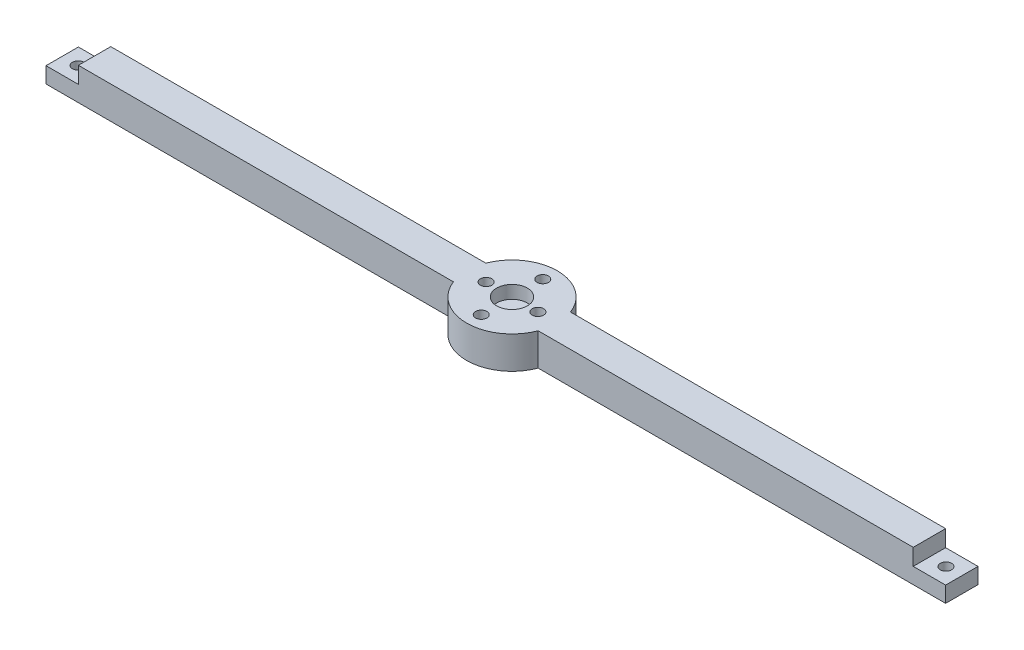
SolidWorks part; units mm, degrees
ref_plane "Front Plane" through (0, 0, 0) normal (0, 0, 1) x (1, 0, 0)
ref_plane "Top Plane" through (0, 0, 0) normal (0, 1, 0) x (1, 0, 0)
ref_plane "Right Plane" through (0, 0, 0) normal (1, 0, 0) x (0, 0, -1)
sketch "Sketch1" plane through (0, 0, 0) normal (0, 1, 0) x (1, 0, 0)
  circle A0 centre (0, 0) radius 14
  dimension "D1" = 28
extrude "Boss-Extrude1" add sketch "Sketch1" along normal blind 10
sketch "Sketch2" plane through (0, 10, 0) normal (0, 1, 0) x (1, 0, 0)
  line L0 (14, 0) -> (149, 0) construction
  line L1 (13.0767, -5) -> (149, -5)
  line L2 (13.0767, 5) -> (149, 5)
  line L4 (149, -5) -> (149, 5)
  line L5 (0, 5) -> (149, 5) construction
  line L6 (0, 0) -> (149, 0) construction
  line L7 (0, -5) -> (149, -5) construction
  circle A1 centre (0, 0) radius 14
  arc A2 (13.0767, -5) -> (13.0767, 5) centre (0, 0) ccw
  point P19 (0, 0)
  dimension "D1" = 149
  dimension "D2" = 5
  dimension "D3" = 5
  dimension "D4" = 0
extrude "Boss-Extrude2" add sketch "Sketch2" against normal up to surface (10 mm away) up to face at (0, 0, 14)
sketch "Sketch4" plane through (0, 0, 5) normal (0, 0, 1) x (1, 0, 0)
  line L0 (149, 0) -> (139, 0) construction
  line L1 (149, 0) -> (13.0767, 0) construction
  line L2 (139, 0) -> (139, 5) construction
  line L3 (139, 5) -> (129, 5) construction
  line L4 (129, 5) -> (129, 10) construction
  line L5 (13.0767, 10) -> (149, 10) construction
  line L6 (138.9, 0) -> (138.9, 4.9)
  line L7 (138.9, 4.9) -> (128.9, 4.9)
  line L8 (128.9, 4.9) -> (128.9, 10)
  line L9 (128.9, 10) -> (149, 10)
  line L10 (149, 10) -> (149, 0)
  line L11 (149, 0) -> (138.9, 0)
  dimension "D1" = 10
  dimension "D2" = 10
  dimension "D3" = 5
  dimension "D4" = 0.1
extrude "Cut-Extrude2" cut sketch "Sketch4" against normal through all
sketch "Sketch6" plane through (0, 4.9, 0) normal (0, 1, 0) x (1, 0, 0)
  line L0 (138.9, 5) -> (128.9, 5) construction
  line L1 (129, 5) -> (139, 5) construction
  line L2 (129, 5) -> (129, -5) construction
  line L3 (129, -5) -> (139, -5) construction
  line L4 (139, 5) -> (139, -5) construction
  line L5 (128.9, -5) -> (138.9, -5) construction
  line L6 (138.9, 5) -> (138.9, -5) construction
  line L7 (128.9, 5) -> (128.9, -5) construction
  line L8 (129, 5) -> (139, -5) construction
  circle A0 centre (134, 0) radius 1.75
  dimension "D3" = 3.5
  dimension "D1" = 0.1
  dimension "D2" = 0.1
extrude "Cut-Extrude4" cut sketch "Sketch6" against normal blind 10
pattern_circular "CirPattern2" count 2 over 180 about axis through (0, 0, 0) along (0, 1, 0) of "Boss-Extrude2", "Cut-Extrude2", "Cut-Extrude4"
sketch "Sketch5" plane through (0, 10, 0) normal (0, 1, 0) x (1, 0, 0)
  line L0 (-8, 0) -> (8, 0) construction
  line L1 (0, -9.5) -> (0, 9.5) construction
  circle A0 centre (0, 9.5) radius 1.75
  circle A1 centre (8, 0) radius 1.75
  circle A2 centre (-8, 0) radius 1.75
  circle A3 centre (0, -9.5) radius 1.75
  point P4 (0, 0)
  point P5 (0, 0)
  dimension "D3" = 3.5
  dimension "D1" = 16
  dimension "D2" = 19
extrude "Cut-Extrude3" cut sketch "Sketch5" against normal through all
sketch "Sketch7" plane through (0, 10, 0) normal (0, 1, 0) x (1, 0, 0)
  circle A0 centre (0, 0) radius 4.75
  dimension "D1" = 9.5
extrude "Cut-Extrude5" cut sketch "Sketch7" against normal blind 4
